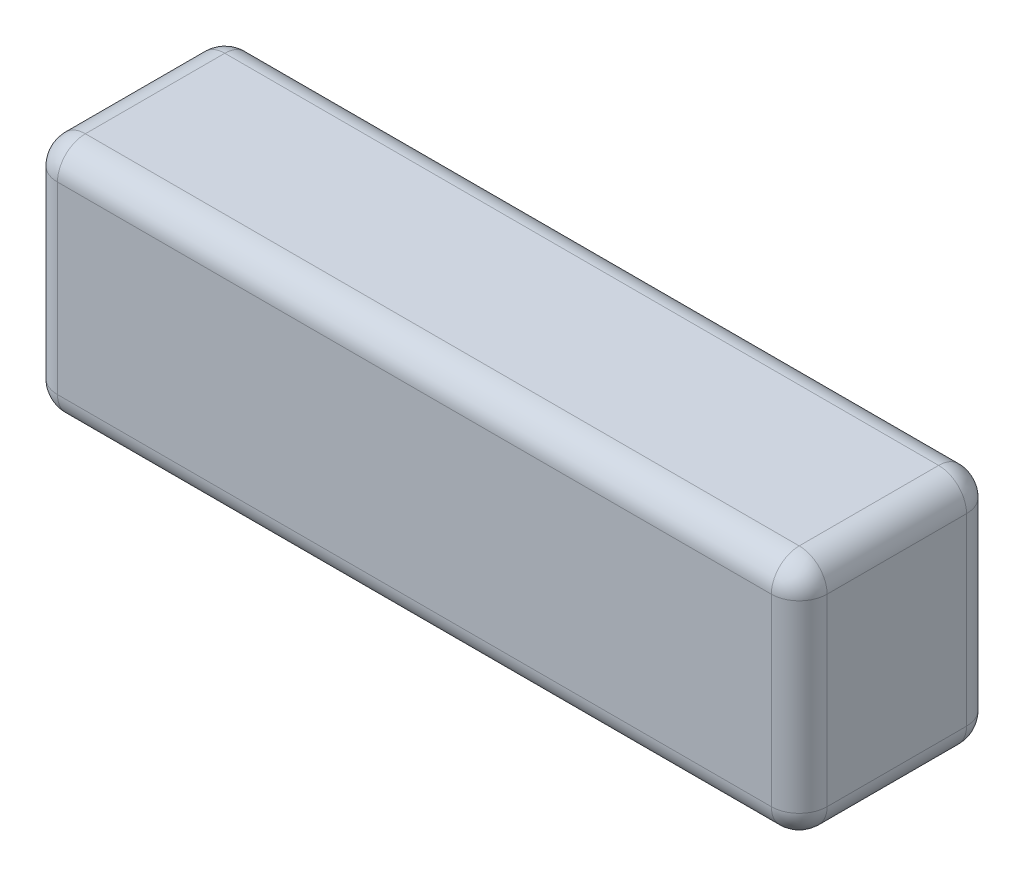
SolidWorks part; units mm, degrees
ref_plane "Front Plane" through (0, 0, 0) normal (0, 0, 1) x (1, 0, 0)
ref_plane "Top Plane" through (0, 0, 0) normal (0, 1, 0) x (1, 0, 0)
ref_plane "Right Plane" through (0, 0, 0) normal (1, 0, 0) x (0, 0, -1)
sketch "Sketch1" plane through (0, 0, 0) normal (0, 0, 1) x (1, 0, 0)
  line L1 (-69, -21.5) -> (69, -21.5)
  line L2 (-69, -21.5) -> (-69, 21.5)
  line L3 (-69, 21.5) -> (69, 21.5)
  line L4 (69, -21.5) -> (69, 21.5)
  line L5 (-69, -21.5) -> (69, 21.5) construction
  line L6 (-69, 21.5) -> (69, -21.5) construction
  point P0 (0, 0)
  dimension "D1" = 138
  dimension "D2" = 43
extrude "Boss-Extrude1" add sketch "Sketch1" along normal blind 35
fillet "Fillet1" radius 5 12 edges at (-69, 21.5, 17.5) (-69, 0, 35) (-69, 0, 0) (-69, -21.5, 17.5) (0, -21.5, 35) (0, -21.5, 0) (69, -21.5, 17.5) (0, 21.5, 0) (69, 0, 0) (69, 0, 35) (0, 21.5, 35) (69, 21.5, 17.5)
